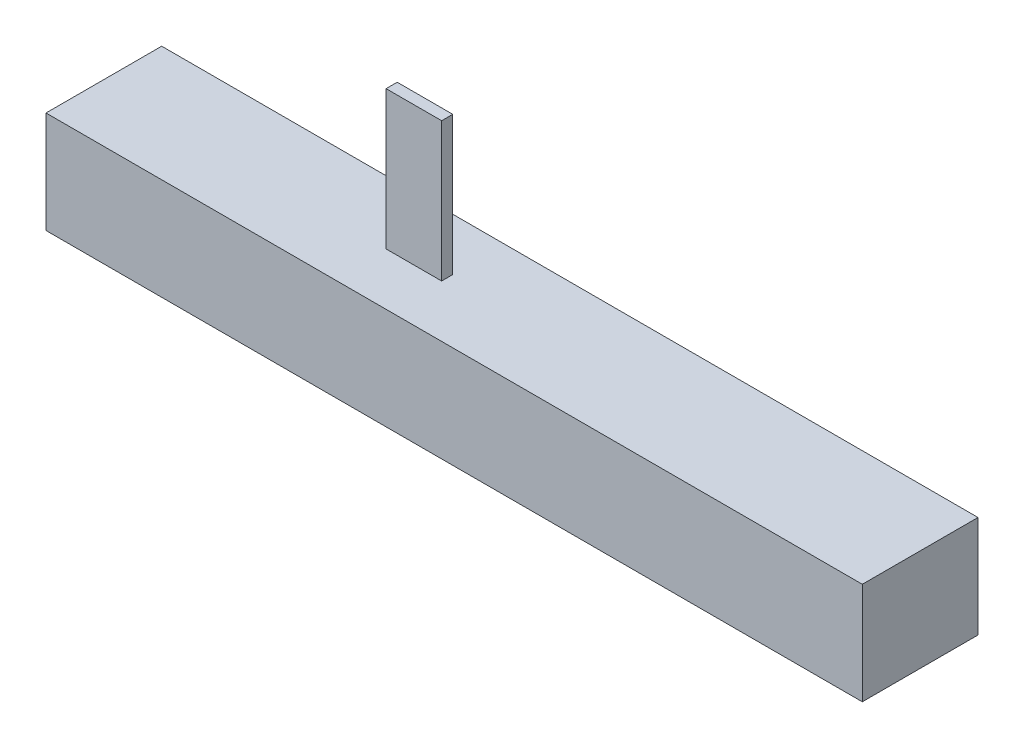
SolidWorks part; units mm, degrees
ref_plane "Front Plane" through (0, 0, 0) normal (0, 0, 1) x (1, 0, 0)
ref_plane "Top Plane" through (0, 0, 0) normal (0, 1, 0) x (1, 0, 0)
ref_plane "Right Plane" through (0, 0, 0) normal (1, 0, 0) x (0, 0, -1)
sketch "Sketch1" plane through (0, 0, 0) normal (0, 0, 1) x (1, 0, 0)
  line L1 (-44.1, -5.5) -> (44.1, -5.5)
  line L2 (-44.1, -5.5) -> (-44.1, 5.5)
  line L3 (-44.1, 5.5) -> (44.1, 5.5)
  line L4 (44.1, -5.5) -> (44.1, 5.5)
  line L5 (-44.1, -5.5) -> (44.1, 5.5) construction
  line L6 (-44.1, 5.5) -> (44.1, -5.5) construction
  point P0 (0, 0)
  dimension "D1" = 88.2
  dimension "D2" = 11
extrude "Boss-Extrude1" add sketch "Sketch1" along normal blind 12.5
sketch "Sketch2" plane through (0, 5.5, 0) normal (0, 1, 0) x (1, 0, 0)
  line L0 (-44.1, -6.25) -> (-10.0026, -6.25) construction
  line L1 (-13.0026, -5.65) -> (-7.0026, -5.65)
  line L2 (-13.0026, -5.65) -> (-13.0026, -6.85)
  line L3 (-13.0026, -6.85) -> (-7.0026, -6.85)
  line L4 (-7.0026, -5.65) -> (-7.0026, -6.85)
  line L5 (-13.0026, -5.65) -> (-7.0026, -6.85) construction
  line L6 (-13.0026, -6.85) -> (-7.0026, -5.65) construction
  line L7 (-44.1, -12.5) -> (-44.1, 0) construction
  point P0 (-10.0026, -6.25)
  dimension "D1" = 1.2
  dimension "D2" = 6
extrude "Boss-Extrude2" add sketch "Sketch2" along normal blind 15
